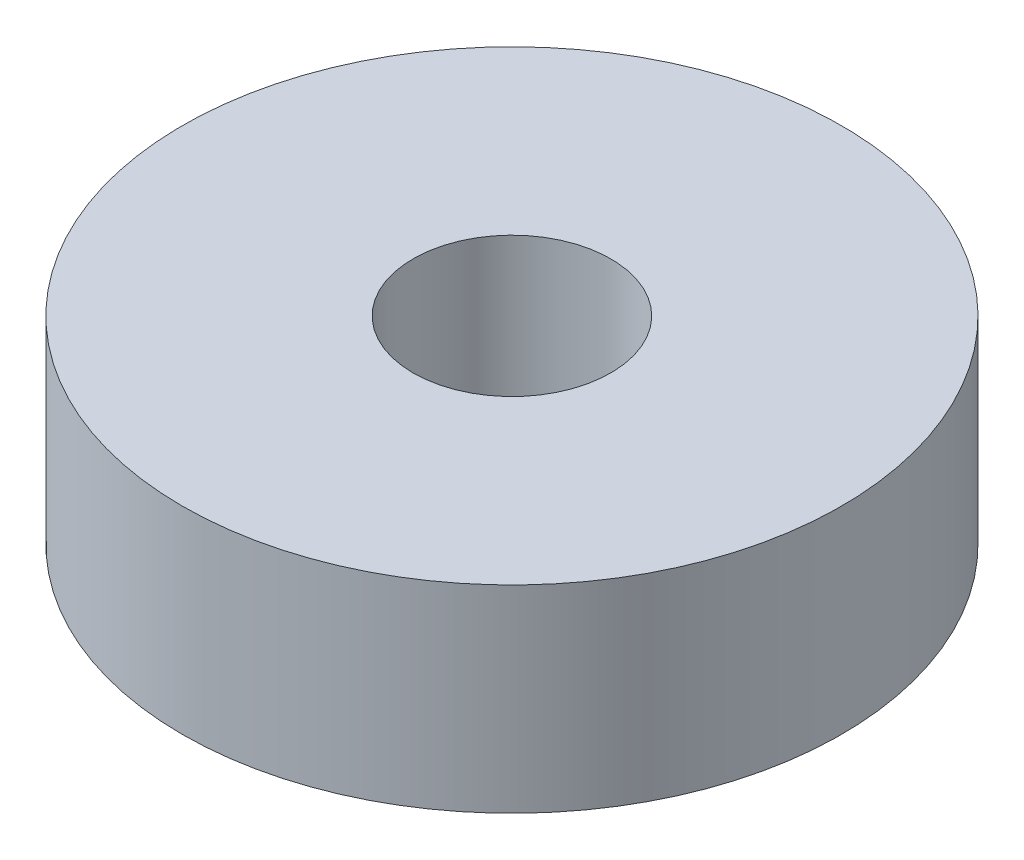
SolidWorks part; units mm, degrees
material "Stainless Steel (ferritic)"
ref_plane "Front Plane" through (0, 0, 0) normal (0, 0, 1) x (1, 0, 0)
ref_plane "Top Plane" through (0, 0, 0) normal (0, 1, 0) x (1, 0, 0)
ref_plane "Right Plane" through (0, 0, 0) normal (1, 0, 0) x (0, 0, -1)
sketch "Sketch1" plane through (0, 0, 0) normal (0, 1, 0) x (1, 0, 0)
  circle A0 centre (0, 0) radius 10
  circle A1 centre (0, 0) radius 3
  dimension "D1" = 20
  dimension "D2" = 6
extrude "Boss-Extrude1" add sketch "Sketch1" along normal blind 6
